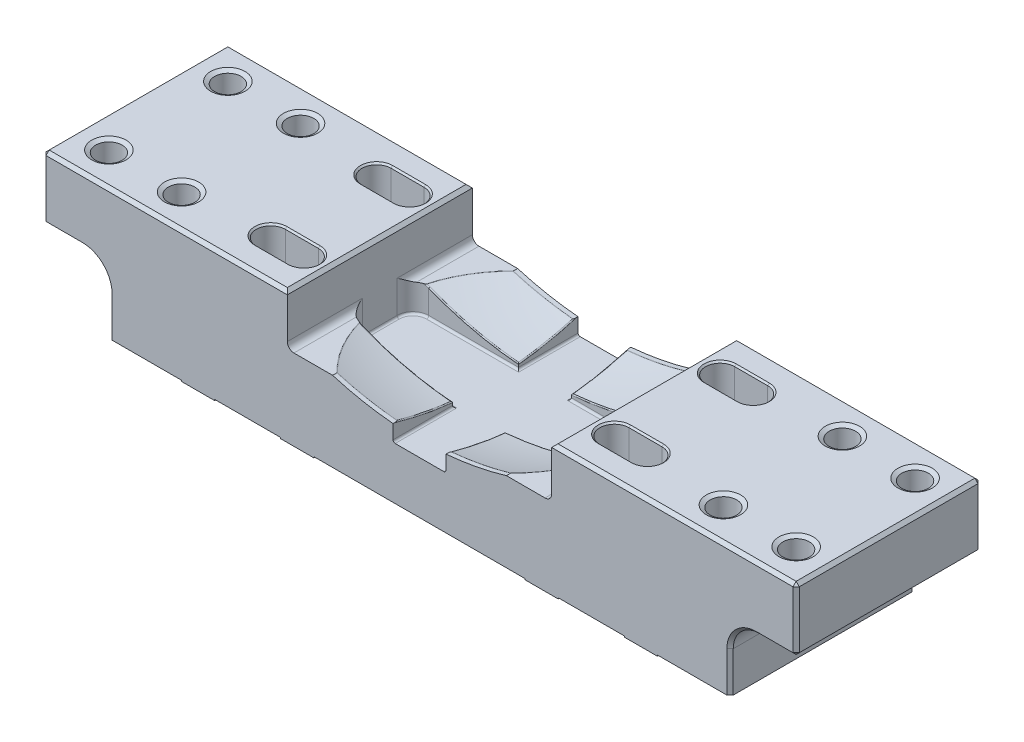
SolidWorks part; units mm, degrees
material "303 SSTL"
ref_plane "Front" through (0, 0, 0) normal (0, 0, 1) x (1, 0, 0)
ref_plane "Top" through (0, 0, 0) normal (0, 1, 0) x (1, 0, 0)
ref_plane "Right" through (0, 0, 0) normal (1, 0, 0) x (0, 0, -1)
sketch "Sketch1" plane through (0, 0, 0) normal (0, 0, 1) x (1, 0, 0)
  line L1 (-180.975, 63.5) -> (180.975, 63.5)
  line L2 (-180.975, 63.5) -> (-180.975, 0)
  line L3 (-180.975, 0) -> (180.975, 0)
  line L4 (180.975, 63.5) -> (180.975, 0)
  dimension "D1" = 361.95
  dimension "D2" = 63.5
extrude "Extrude1" add sketch "Sketch1" along normal mid plane 88.9
sketch "Sketch2" plane through (0, 0, 0) normal (0, 0, 1) x (1, 0, 0)
  line L0 (0, -34.925) -> (0, 34.925) construction
  line L1 (-63.5, 41.1644) -> (-63.5, 63.5)
  line L2 (180.975, 63.5) -> (-180.975, 63.5) construction
  line L3 (-63.5, 63.5) -> (63.5, 63.5)
  line L4 (63.5, 63.5) -> (63.5, 41.1644)
  line L5 (-180.975, 0) -> (180.975, 0) construction
  line L6 (0, 179.705) -> (41.8632, 179.705) construction
  arc A0 (-63.5, 41.1644) -> (63.5, 41.1644) centre (0, 179.705) ccw
  point P5 (0, 27.305)
  dimension "D2" = 152.4
  dimension "D1" = 27.305
  dimension "D3" = 127
revolve "Cut-Revolve1" cut sketch "Sketch2" angle 360 about L6
sketch "Sketch3" plane through (0, 0, 0) normal (0, 0, 1) x (1, 0, 0)
  line L0 (-63.5, 63.5) -> (-180.975, 63.5) construction
  line L1 (-63.5, 48.4887) -> (63.5, 48.4887)
  line L2 (-63.5, 48.4887) -> (-63.5, 39.37)
  line L3 (-63.5, 39.37) -> (63.5, 39.37)
  line L4 (63.5, 48.4887) -> (63.5, 39.37)
  dimension "D1" = 24.13
extrude "Extrude2" cut sketch "Sketch3" against normal through all and the other way through all
sketch "Sketch4" plane through (0, 39.37, 0) normal (0, 1, 0) x (1, 0, 0)
  line L0 (-63.5, 15.875) -> (-63.5, -15.875)
  line L1 (-63.5, -44.45) -> (-63.5, 44.45) construction
  line L2 (-63.5, 44.45) -> (-63.5, -44.45) construction
  line L3 (-63.5, -15.875) -> (-12.7, -15.875)
  line L4 (-12.7, -15.875) -> (-12.7, -44.45)
  line L5 (-39.4467, -44.45) -> (39.4467, -44.45) construction
  line L6 (-12.7, -44.45) -> (12.7, -44.45)
  line L7 (12.7, -44.45) -> (12.7, -15.875)
  line L8 (12.7, -15.875) -> (63.5, -15.875)
  line L9 (63.5, 44.45) -> (63.5, -44.45) construction
  line L10 (63.5, -15.875) -> (63.5, 15.875)
  line L11 (63.5, 44.45) -> (63.5, -44.45) construction
  line L12 (63.5, 15.875) -> (12.7, 15.875)
  line L13 (12.7, 15.875) -> (12.7, 44.45)
  line L14 (39.4467, 44.45) -> (-39.4467, 44.45) construction
  line L15 (12.7, 44.45) -> (-12.7, 44.45)
  line L16 (-12.7, 44.45) -> (-12.7, 15.875)
  line L17 (-12.7, 15.875) -> (-63.5, 15.875)
  line L18 (0, -34.925) -> (0, 34.925) construction
  line L19 (-34.925, 0) -> (34.925, 0) construction
  point P6 (0, 44.45)
  point P27 (-63.5, 0)
  dimension "D1" = 31.75
  dimension "D2" = 25.4
extrude "Extrude4" cut sketch "Sketch4" against normal offset from surface (13.335 mm away) 37.465 up to face at (-122.2375, 63.5, 0)
sketch "Sketch5" plane through (0, 0, 0) normal (0, 0, 1) x (1, 0, 0)
  line L0 (-180.975, 63.5) -> (-180.975, 0) construction
  line L1 (-180.975, 33.02) -> (-149.225, 33.02)
  line L2 (-180.975, 33.02) -> (-180.975, 0)
  line L3 (-180.975, 0) -> (-149.225, 0)
  line L4 (-149.225, 33.02) -> (-149.225, 0)
  line L5 (-180.975, 0) -> (180.975, 0) construction
  line L6 (180.975, 0) -> (180.975, 63.5) construction
  line L7 (180.975, 33.02) -> (149.225, 33.02)
  line L8 (180.975, 33.02) -> (180.975, 0)
  line L9 (180.975, 0) -> (149.225, 0)
  line L10 (149.225, 33.02) -> (149.225, 0)
  dimension "D1" = 33.02
  dimension "D2" = 298.45
extrude "Extrude5" cut sketch "Sketch5" against normal through all and the other way through all
sketch "Sketch6" plane through (0, 0, 0) normal (0, -1, 0) x (1, 0, 0)
  line L0 (-149.225, 44.45) -> (-149.225, -44.45)
  line L1 (-149.225, -44.45) -> (-114.3, -44.45)
  line L2 (-149.225, -44.45) -> (149.225, -44.45) construction
  line L3 (-114.3, -44.45) -> (-114.3, -12.7)
  line L4 (-114.3, -12.7) -> (-98.425, -12.7)
  line L5 (-98.425, -12.7) -> (-98.425, -44.45)
  line L6 (-98.425, -44.45) -> (-66.675, -44.45)
  line L7 (-66.675, -44.45) -> (-66.675, -12.7)
  line L8 (-66.675, -12.7) -> (-50.8, -12.7)
  line L9 (-50.8, -12.7) -> (-50.8, -44.45)
  line L10 (-50.8, 44.45) -> (50.8, 44.45)
  line L11 (149.225, -44.45) -> (149.225, 44.45)
  line L12 (50.8, 44.45) -> (50.8, 12.7)
  line L13 (-149.225, 44.45) -> (149.225, 44.45) construction
  line L14 (-50.8, 44.45) -> (-50.8, 12.7)
  line L15 (-50.8, 12.7) -> (-66.675, 12.7)
  line L16 (-66.675, 12.7) -> (-66.675, 44.45)
  line L17 (-66.675, 44.45) -> (-98.425, 44.45)
  line L18 (-98.425, 44.45) -> (-98.425, 12.7)
  line L19 (-98.425, 12.7) -> (-114.3, 12.7)
  line L20 (-114.3, 12.7) -> (-114.3, 44.45)
  line L21 (-114.3, 44.45) -> (-149.225, 44.45)
  line L22 (50.8, 12.7) -> (66.675, 12.7)
  line L24 (66.675, 12.7) -> (66.675, 44.45)
  line L25 (66.675, 44.45) -> (98.425, 44.45)
  line L26 (98.425, 44.45) -> (98.425, 12.7)
  line L27 (98.425, 12.7) -> (114.3, 12.7)
  line L28 (114.3, 12.7) -> (114.3, 44.45)
  line L29 (114.3, 44.45) -> (149.225, 44.45)
  line L30 (149.225, -44.45) -> (114.3, -44.45)
  line L31 (114.3, -44.45) -> (114.3, -12.7)
  line L32 (114.3, -12.7) -> (98.425, -12.7)
  line L33 (98.425, -12.7) -> (98.425, -44.45)
  line L34 (98.425, -44.45) -> (66.675, -44.45)
  line L35 (66.675, -44.45) -> (66.675, -12.7)
  line L36 (66.675, -12.7) -> (50.8, -12.7)
  line L37 (50.8, -12.7) -> (50.8, -44.45)
  line L38 (50.8, -44.45) -> (-50.8, -44.45)
  line L39 (-98.425, 12.7) -> (-66.675, 12.7) construction
  line L40 (66.675, 12.7) -> (98.425, 12.7) construction
  point P35 (0, 44.45)
  dimension "D1" = 31.75
  dimension "D2" = 15.875
  dimension "D3" = 25.4
  dimension "D4" = 101.6
extrude "Extrude6" cut sketch "Sketch6" against normal blind 1.016
fillet "Fillet1" radius 12.7 2 edges at (149.225, 33.02, 0) (-149.225, 33.02, 0)
fillet "Fillet2" radius 7.62 4 edges at (63.5, 32.7025, 15.875) (63.5, 32.7025, -15.875) (-63.5, 32.7025, 15.875) (-63.5, 32.7025, -15.875)
fillet "Fillet3" radius 3.175 4 edges at (63.5, 39.37, 26.3525) (63.5, 39.37, -26.3525) (-63.5, 39.37, 26.3525) (-63.5, 39.37, -26.3525)
fillet "Fillet4" radius 1.016 14 edges at (-34.29, 26.035, -15.875) (-61.2682, 26.035, -13.6432) (-34.29, 26.035, 15.875) (-61.2682, 26.035, 13.6432) (34.29, 26.035, 15.875) (61.2682, 26.035, 13.6432) (63.5, 26.035, 0) (61.2682, 26.035, -13.6432) (-12.7, 26.035, -30.1625) (-63.5, 26.035, 0) (-12.7, 26.035, 30.1625) (12.7, 26.035, 30.1625) (34.29, 26.035, -15.875) (12.7, 26.035, -30.1625)
hole_wizard "1/2-13 Tapped Hole1" positions "Sketch8" profile "Sketch7" tap size "1/2-13" standard "Ansi Inch" end condition through all
sketch "Sketch8" plane through (0, 63.5, 0) normal (0, 1, 0) x (-1, 0, 0)
  line L1 (-165.1, 28.575) -> (-130.175, 28.575) construction
  line L2 (-165.1, 28.575) -> (-165.1, -28.575) construction
  line L3 (-165.1, -28.575) -> (-130.175, -28.575) construction
  line L4 (-130.175, 28.575) -> (-130.175, -28.575) construction
  line L6 (130.175, 28.575) -> (165.1, 28.575) construction
  line L7 (130.175, 28.575) -> (130.175, -28.575) construction
  line L8 (130.175, -28.575) -> (165.1, -28.575) construction
  line L9 (165.1, 28.575) -> (165.1, -28.575) construction
  line L11 (34.925, 0) -> (-34.925, 0) construction
  line L14 (-130.175, 28.575) -> (130.175, 28.575) construction
  line L17 (0, 34.925) -> (0, -34.925) construction
  point P0 (165.1, -28.575)
  point P1 (165.1, 28.575)
  point P3 (130.175, 28.575)
  point P5 (130.175, -28.575)
  point P7 (-165.1, 28.575)
  point P9 (-130.175, 28.575)
  point P11 (-130.175, -28.575)
  point P13 (-165.1, -28.575)
  point P498 (-130.175, 0)
  point P512 (0, 28.575)
  dimension "D1" = 34.925
  dimension "D2" = 57.15
  dimension "D3" = 260.35
sketch "Sketch7" plane through (-165.1, 63.5, -28.575) normal (1, 0, 0) x (0, 0, 1)
  line L0 (0, 0) -> (0, 63.5)
  line L1 (0, 63.5) -> (5.3581, 63.5)
  line L3 (5.3581, 63.5) -> (5.3581, 38.1)
  line L4 (6.35, 38.1) -> (5.3581, 38.1)
  line L5 (6.35, 38.1) -> (6.35, 1.0999)
  line L6 (6.35, 1.0999) -> (8.255, 0)
  line L7 (8.255, 0) -> (0, 0)
  line L8 (-6.35, 1.0999) -> (-8.255, 0) construction
  line L11 (0, -6.35) -> (0, 107.95) construction
  dimension "Thru Tap Drill Dia." = 10.7163
  dimension "Thru Tap Drill Depth" = 63.5
  dimension "Thread Major Dia." = 12.7
  dimension "Thread Depth" = 38.1
  dimension "Near C'Sink Dia." = 16.51
  dimension "Near C'Sink Angle" = 120
sketch "Sketch9" plane through (0, 63.5, 0) normal (0, 1, 0) x (1, 0, 0)
  line L0 (-90.4875, 25.4) -> (-74.6125, 25.4) construction
  line L1 (-90.4875, 32.385) -> (-74.6125, 32.385)
  line L2 (-90.4875, 18.415) -> (-74.6125, 18.415)
  line L3 (-90.4875, -25.4) -> (-74.6125, -25.4) construction
  line L4 (-90.4875, -18.415) -> (-74.6125, -18.415)
  line L5 (-90.4875, -32.385) -> (-74.6125, -32.385)
  line L6 (74.6125, 25.4) -> (90.4875, 25.4) construction
  line L7 (74.6125, 32.385) -> (90.4875, 32.385)
  line L8 (74.6125, 18.415) -> (90.4875, 18.415)
  line L9 (74.6125, -25.4) -> (90.4875, -25.4) construction
  line L10 (74.6125, -18.415) -> (90.4875, -18.415)
  line L11 (74.6125, -32.385) -> (90.4875, -32.385)
  line L12 (-82.55, 25.4) -> (-82.55, -25.4) construction
  line L13 (82.55, 25.4) -> (82.55, -25.4) construction
  line L14 (-82.55, 0) -> (82.55, 0) construction
  arc A0 (-90.4875, 32.385) -> (-90.4875, 18.415) centre (-90.4875, 25.4) ccw
  arc A1 (-74.6125, 18.415) -> (-74.6125, 32.385) centre (-74.6125, 25.4) ccw
  arc A2 (-90.4875, -18.415) -> (-90.4875, -32.385) centre (-90.4875, -25.4) ccw
  arc A3 (-74.6125, -32.385) -> (-74.6125, -18.415) centre (-74.6125, -25.4) ccw
  arc A4 (74.6125, 32.385) -> (74.6125, 18.415) centre (74.6125, 25.4) ccw
  arc A5 (90.4875, 18.415) -> (90.4875, 32.385) centre (90.4875, 25.4) ccw
  arc A6 (74.6125, -18.415) -> (74.6125, -32.385) centre (74.6125, -25.4) ccw
  arc A7 (90.4875, -32.385) -> (90.4875, -18.415) centre (90.4875, -25.4) ccw
  point P2 (-82.55, 25.4)
  point P7 (-82.55, -25.4)
  point P14 (82.55, 25.4)
  point P21 (82.55, -25.4)
  dimension "D1" = 50.8
  dimension "D2" = 13.97
  dimension "D3" = 165.1
  dimension "D4" = 15.875
extrude "Extrude7" cut sketch "Sketch9" against normal through all
sketch "Sketch10" plane through (0, 0, 0) normal (0, 0, 1) x (1, 0, 0)
  line L0 (0, -34.925) -> (0, 34.925) construction
  line L1 (48.895, 0) -> (-48.895, 0) construction
  line L2 (-41.755, 39.37) -> (41.755, 39.37)
  line L3 (-60.325, 39.37) -> (-39.4467, 39.37) construction
  line L4 (39.4467, 39.37) -> (60.325, 39.37) construction
  circle A0 centre (0, 179.324) radius 146.05 construction
  arc A1 (-41.755, 39.37) -> (41.755, 39.37) centre (0, 179.324) ccw
  dimension "D1" = 292.1
  dimension "D2" = 179.324
extrude "Extrude8" cut sketch "Sketch10" against normal through all and the other way through all
chamfer "Chamfer1" distance 0.762 angle 45 16 edges at (82.55, 63.5, 32.385) (97.4725, 63.5, 25.4) (67.6275, 63.5, 25.4) (82.55, 63.5, 18.415) (82.55, 63.5, -18.415) (97.4725, 63.5, -25.4) (67.6275, 63.5, -25.4) (82.55, 63.5, -32.385) (-82.55, 63.5, 32.385) (-67.6275, 63.5, 25.4) (-97.4725, 63.5, 25.4) (-82.55, 63.5, 18.415) (-82.55, 63.5, -18.415) (-67.6275, 63.5, -25.4) (-97.4725, 63.5, -25.4) (-82.55, 63.5, -32.385)
chamfer "Chamfer2" distance 1.524 angle 45 26 edges at (180.975, 48.26, -44.45) (180.975, 33.02, 0) (180.975, 48.26, 44.45) (180.975, 63.5, 0) (122.2375, 63.5, 44.45) (122.2375, 63.5, -44.45) (63.5, 63.5, 0) (-63.5, 63.5, 0) (-122.2375, 63.5, 44.45) (-122.2375, 63.5, -44.45) (-180.975, 33.02, 0) (-180.975, 48.26, -44.45) (-180.975, 63.5, 0) (-180.975, 48.26, 44.45) (149.225, 10.668, -44.45) (149.225, 10.668, 44.45) (152.9447, 29.3003, -44.45) (152.9447, 29.3003, 44.45) (171.45, 33.02, -44.45) (171.45, 33.02, 44.45) (-149.225, 10.668, -44.45) (-149.225, 10.668, 44.45) (-152.9447, 29.3003, -44.45) (-152.9447, 29.3003, 44.45) (-171.45, 33.02, -44.45) (-171.45, 33.02, 44.45)
chamfer "Chamfer3" distance 0.508 angle 45 32 edges at (50.8, 0, -28.575) (58.7375, 0, -12.7) (66.675, 0, -28.575) (58.7375, 0, -44.45) (98.425, 0, -28.575) (106.3625, 0, -12.7) (114.3, 0, -28.575) (106.3625, 0, -44.45) (114.3, 0, 28.575) (106.3625, 0, 12.7) (98.425, 0, 28.575) (106.3625, 0, 44.45) (66.675, 0, 28.575) (58.7375, 0, 12.7) (50.8, 0, 28.575) (58.7375, 0, 44.45) (-66.675, 0, -28.575) (-58.7375, 0, -12.7) (-50.8, 0, -28.575) (-58.7375, 0, -44.45) (-114.3, 0, -28.575) (-106.3625, 0, -12.7) (-98.425, 0, -28.575) (-106.3625, 0, -44.45) (-50.8, 0, 28.575) (-58.7375, 0, 12.7) (-66.675, 0, 28.575) (-58.7375, 0, 44.45) (-98.425, 0, 28.575) (-106.3625, 0, 12.7) (-114.3, 0, 28.575) (-106.3625, 0, 44.45)
fillet "Fillet5" radius 0.508 20 edges at (-34.6631, 32.1509, -15.875) (-51.279, 39.37, -30.0386) (-12.7, 30.6631, -29.1714) (34.6631, 32.1509, 15.875) (51.279, 39.37, 30.0386) (12.7, 30.6631, 29.1714) (34.6631, 32.1509, -15.875) (12.7, 30.6631, -29.1714) (51.279, 39.37, -30.0386) (-34.6631, 32.1509, 15.875) (-12.7, 30.6631, 29.1714) (-51.279, 39.37, 30.0386)
